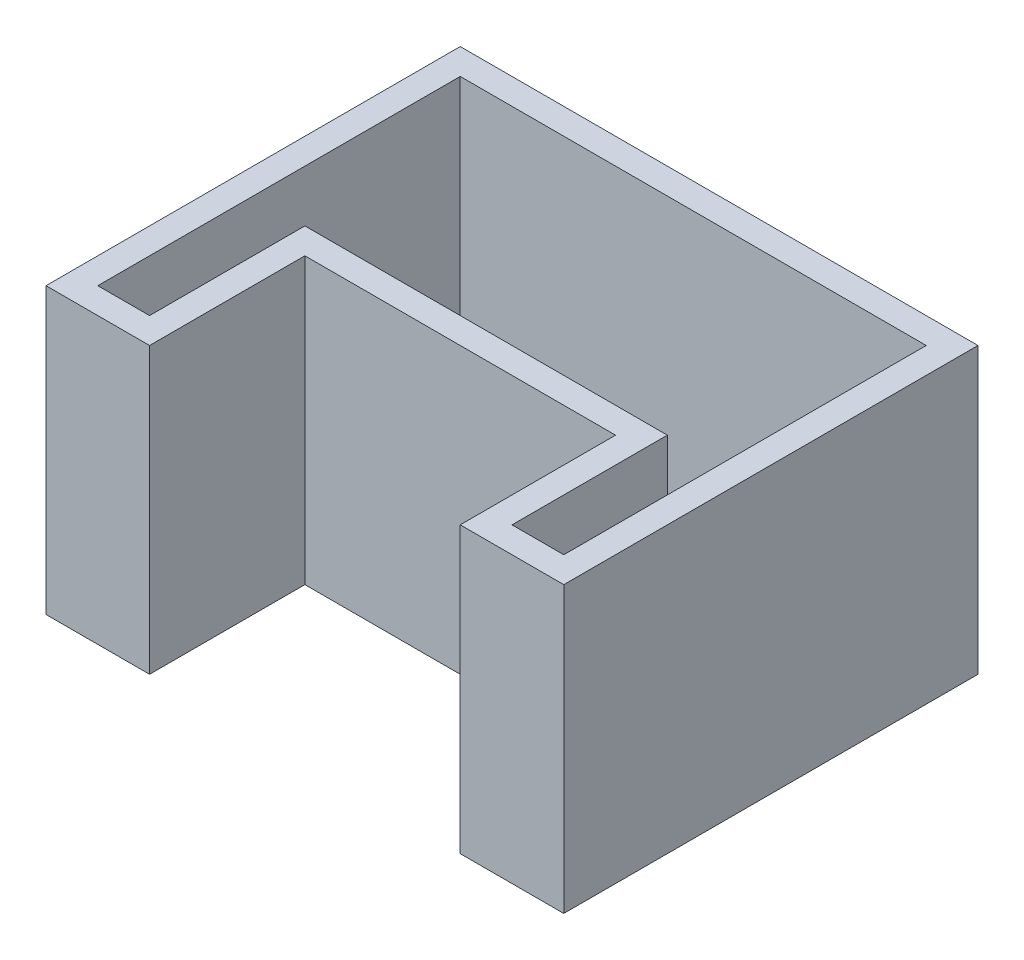
SolidWorks part; units mm, degrees
material "PUR"
ref_plane "Front Plane" through (0, 0, 0) normal (0, 0, 1) x (1, 0, 0)
ref_plane "Top Plane" through (0, 0, 0) normal (0, 1, 0) x (1, 0, 0)
ref_plane "Right Plane" through (0, 0, 0) normal (1, 0, 0) x (0, 0, -1)
sketch "Sketch2" plane through (0, 0, 0) normal (0, 1, 0) x (1, 0, 0)
  line L0 (-60, -80) -> (-60, -20)
  line L1 (-100, 80) -> (100, 80)
  line L2 (-100, 80) -> (-100, -80)
  line L3 (-100, -80) -> (-60, -80)
  line L4 (100, 80) -> (100, -80)
  line L5 (-100, 80) -> (100, -80) construction
  line L6 (-100, -80) -> (100, 80) construction
  line L7 (-60, -20) -> (60, -20)
  line L8 (60, -20) -> (60, -80)
  line L9 (60, -80) -> (100, -80)
  point P0 (0, 0)
  dimension "D1" = 160
  dimension "D2" = 200
  dimension "D3" = 60
  dimension "D4" = 120
  dimension "D5" = 40
extrude "Boss-Extrude1" add sketch "Sketch2" along normal blind 10
sketch "Sketch3" plane through (0, 10, 0) normal (0, 1, 0) x (1, 0, 0)
  line L0 (-60, -80) -> (-60, -20)
  line L1 (-60, -20) -> (60, -20)
  line L2 (60, -20) -> (60, -80)
  line L3 (60, -20) -> (60, -80) construction
  line L4 (60, -80) -> (100, -80)
  line L5 (100, -80) -> (100, 80)
  line L6 (100, 80) -> (-100, 80)
  line L7 (-100, 80) -> (-100, -80)
  line L8 (-100, -80) -> (-60, -80)
  line L9 (90, 70) -> (-90, 70)
  line L10 (-90, 70) -> (-90, -70)
  line L11 (-90, -70) -> (-70, -70)
  line L12 (-70, -70) -> (-70, -10)
  line L13 (-70, -10) -> (70, -10)
  line L14 (70, -10) -> (70, -70)
  line L15 (70, -70) -> (90, -70)
  line L16 (90, -70) -> (90, 70)
  dimension "D1" = 10
extrude "Boss-Extrude2" add sketch "Sketch3" along normal blind 100
sketch "Sketch4" plane through (0, 10, 0) normal (0, 1, 0) x (1, 0, 0)
  circle A0 centre (0, 23.078) radius 5
  point P2 (0, 0)
  dimension "D1" = 10
extrude "Cut-Extrude1" cut sketch "Sketch4" against normal blind 10
